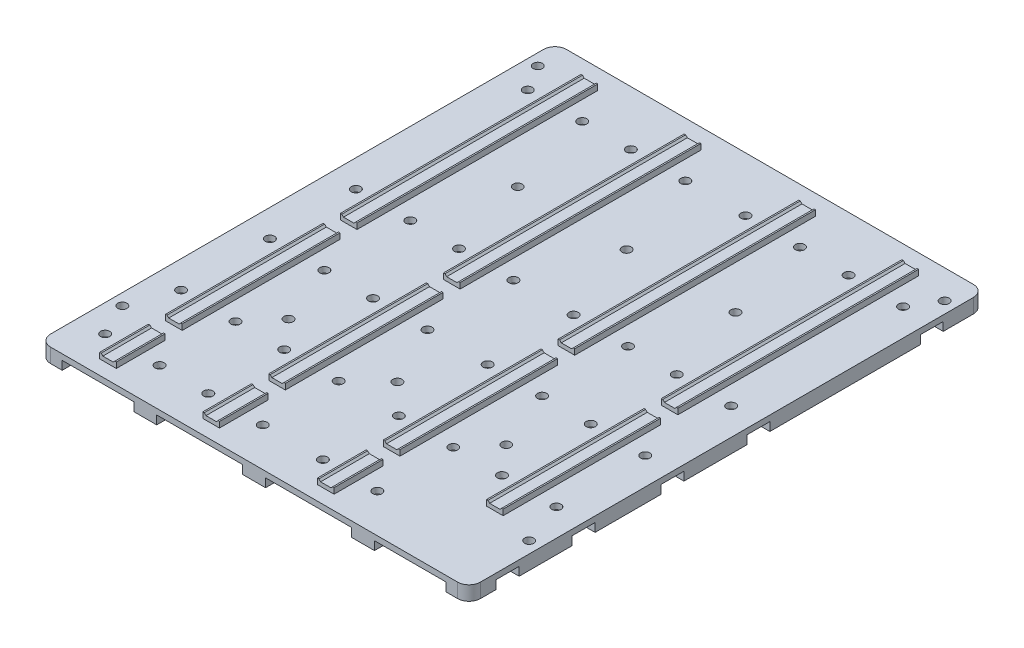
SolidWorks part; units mm, degrees
ref_plane "Front Plane" through (0, 0, 0) normal (0, 0, 1) x (1, 0, 0)
ref_plane "Top Plane" through (0, 0, 0) normal (0, 1, 0) x (1, 0, 0)
ref_plane "Right Plane" through (0, 0, 0) normal (1, 0, 0) x (0, 0, -1)
sketch "Sketch1" plane through (0, 0, 0) normal (0, 1, 0) x (1, 0, 0)
  line L1 (-75, -90) -> (75, -90)
  line L2 (-75, -90) -> (-75, 90)
  line L3 (-75, 90) -> (75, 90)
  line L4 (75, -90) -> (75, 90)
  line L5 (-75, -90) -> (75, 90) construction
  line L6 (-75, 90) -> (75, -90) construction
  point P0 (0, 0)
  dimension "D1" = 150
  dimension "D2" = 180
extrude "Boss-Extrude1" add sketch "Sketch1" along normal blind 2
sketch "Sketch2" plane through (0, 2, 0) normal (0, 1, 0) x (1, 0, 0)
  line L0 (-75, -90) -> (75, -90) construction
  line L1 (-58.9, -7) -> (-53.1, -7)
  line L2 (-58.9, -7) -> (-58.9, -85)
  line L3 (-58.9, -85) -> (-53.1, -85)
  line L4 (-53.1, -7) -> (-53.1, -85)
  line L5 (-22.9, -7) -> (-17.1, -7)
  line L6 (-22.9, -7) -> (-22.9, -85)
  line L7 (-22.9, -85) -> (-17.1, -85)
  line L8 (-17.1, -7) -> (-17.1, -85)
  line L9 (17.1, -7) -> (22.9, -7)
  line L10 (17.1, -7) -> (17.1, -85)
  line L11 (17.1, -85) -> (22.9, -85)
  line L12 (22.9, -7) -> (22.9, -85)
  line L13 (53.1, -7) -> (58.9, -7)
  line L14 (53.1, -7) -> (53.1, -85)
  line L15 (53.1, -85) -> (58.9, -85)
  line L16 (58.9, -7) -> (58.9, -85)
  line L17 (-75, 90) -> (-75, -90) construction
  line L18 (75, -90) -> (75, 90) construction
  line L19 (75, 90) -> (-75, 90) construction
  line L20 (-58.9, -62) -> (58.9, -62)
  line L21 (-58.9, -62) -> (-58.9, -68)
  line L22 (-58.9, -68) -> (58.9, -68)
  line L23 (58.9, -62) -> (58.9, -68)
  line L24 (-58.9, -1) -> (-53.1, -1)
  line L25 (-58.9, -1) -> (-58.9, 83)
  line L26 (-58.9, 83) -> (-53.1, 83)
  line L27 (-53.1, -1) -> (-53.1, 83)
  line L28 (-22.9, -1) -> (-17.1, -1)
  line L29 (-22.9, -1) -> (-22.9, 83)
  line L30 (-22.9, 83) -> (-17.1, 83)
  line L31 (-17.1, -1) -> (-17.1, 83)
  line L32 (17.1, -1) -> (22.9, -1)
  line L33 (17.1, -1) -> (17.1, 83)
  line L34 (17.1, 83) -> (22.9, 83)
  line L35 (22.9, -1) -> (22.9, 83)
  line L36 (53.1, -1) -> (58.9, -1)
  line L37 (53.1, -1) -> (53.1, 83)
  line L38 (53.1, 83) -> (58.9, 83)
  line L39 (58.9, -1) -> (58.9, 83)
  dimension "D1" = 5
  dimension "D2" = 16.1
  dimension "D3" = 5.8
  dimension "D4" = 78
  dimension "D5" = 52.1
  dimension "D6" = 5.8
  dimension "D7" = 5
  dimension "D8" = 5
  dimension "D9" = 5.8
  dimension "D10" = 5.8
  dimension "D11" = 5
  dimension "D12" = 16.1
  dimension "D13" = 52.1
  dimension "D14" = 22
  dimension "D15" = 6
  dimension "D16" = 16.1
  dimension "D17" = 5.8
  dimension "D18" = 6
  dimension "D19" = 7
  dimension "D20" = 7
  dimension "D21" = 7
  dimension "D22" = 7
  dimension "D23" = 52.1
  dimension "D24" = 16.1
  dimension "D25" = 52.1
  dimension "D26" = 5.8
  dimension "D27" = 5.8
  dimension "D28" = 5.8
  dimension "D29" = 6
  dimension "D30" = 6
  dimension "D31" = 6
extrude "Boss-Extrude2" add sketch "Sketch2" along normal blind 2 contours L2 L20 L4 L1 | L22 L2 L3 L4 | L6 L20 L8 L5 | L22 L6 L7 L8 | L10 L20 L12 L9 | L22 L10 L11 L12 | L14 L20 L16 L13 | L25 L24 L27 L26 | L29 L28 L31 L30 | L33 L32 L35 L34 | L37 L36 L39 L38
sketch "Sketch3" plane through (0, 2, 0) normal (0, 1, 0) x (1, 0, 0)
  line L0 (-75, -90) -> (75, -90) construction
  line L1 (-56, -7) -> (-56, -62) construction
  line L2 (-58.9, -7) -> (-53.1, -7) construction
  line L3 (-58.9, -68) -> (-58.9, -85) construction
  line L4 (-53.1, -68) -> (-53.1, -85) construction
  line L5 (17.1, -68) -> (17.1, -85) construction
  line L6 (22.9, -68) -> (22.9, -85) construction
  line L9 (-22.9, -68) -> (-22.9, -85) construction
  line L10 (-17.1, -68) -> (-17.1, -85) construction
  line L11 (-58.9, -62) -> (-53.1, -62) construction
  line L12 (-56, -1) -> (-56, 83) construction
  line L13 (-58.9, -1) -> (-53.1, -1) construction
  line L16 (-22.9, -7) -> (-22.9, -62) construction
  line L17 (-17.1, -7) -> (-17.1, -62) construction
  line L18 (17.1, -7) -> (17.1, -62) construction
  line L19 (22.9, -7) -> (22.9, -62) construction
  line L20 (53.1, -7) -> (53.1, -62) construction
  line L21 (58.9, -7) -> (58.9, -62) construction
  line L22 (-58.9, 83) -> (-53.1, 83) construction
  line L25 (-22.9, -1) -> (-22.9, 83) construction
  line L26 (-17.1, -1) -> (-17.1, 83) construction
  line L27 (17.1, -1) -> (17.1, 83) construction
  line L28 (22.9, -1) -> (22.9, 83) construction
  line L29 (53.1, -1) -> (53.1, 83) construction
  line L30 (58.9, -1) -> (58.9, 83) construction
  line L33 (-58.9, 83) -> (-53.1, 83) construction
  line L34 (-58.9, -7) -> (-53.1, -7) construction
  line L35 (-58.9, -7) -> (-58.9, -62) construction
  line L36 (-53.1, -7) -> (-53.1, -62) construction
  line L37 (-17.1, -7) -> (-17.1, -62) construction
  line L38 (17.1, -7) -> (17.1, -62) construction
  line L39 (22.9, -7) -> (22.9, -62) construction
  line L40 (58.9, -7) -> (58.9, -62) construction
  line L41 (-58.9, -1) -> (-58.9, 83) construction
  line L42 (-53.1, -1) -> (-53.1, 83) construction
  line L43 (22.9, -1) -> (22.9, 83) construction
  line L44 (53.1, -1) -> (53.1, 83) construction
  circle A0 centre (-65.5, -76.5) radius 1.6
  circle A1 centre (-46.5, -76.5) radius 1.6
  circle A2 centre (-29.5, -76.5) radius 1.6
  circle A3 centre (-10.5, -76.5) radius 1.6
  circle A4 centre (10.5, -76.5) radius 1.6
  circle A5 centre (29.5, -76.5) radius 1.6
  circle A10 centre (-65.5, -50) radius 1.6
  circle A11 centre (-46.5, -50) radius 1.6
  circle A12 centre (-29.5, -50) radius 1.6
  circle A13 centre (-10.5, -50) radius 1.6
  circle A17 centre (10.5, -50) radius 1.6
  circle A18 centre (29.5, -50) radius 1.6
  circle A22 centre (46.5, -50) radius 1.6
  circle A23 centre (65.5, -50) radius 1.6
  circle A24 centre (65.5, 11) radius 1.6
  circle A25 centre (-65.5, 11) radius 1.6
  circle A26 centre (10.5, 11) radius 1.6
  circle A27 centre (-29.5, 11) radius 1.6
  circle A28 centre (-46.5, 11) radius 1.6
  circle A29 centre (46.5, 11) radius 1.6
  circle A30 centre (29.5, 11) radius 1.6
  circle A31 centre (-10.5, 11) radius 1.6
  circle A32 centre (10.5, 71) radius 1.6
  circle A33 centre (65.5, 71) radius 1.6
  circle A34 centre (29.5, 71) radius 1.6
  circle A35 centre (-46.5, 71) radius 1.6
  circle A36 centre (-65.5, 71) radius 1.6
  circle A37 centre (-29.5, 71) radius 1.6
  circle A38 centre (-10.5, 71) radius 1.6
  circle A39 centre (46.5, 71) radius 1.6
  circle A40 centre (-65.5, -19) radius 1.6
  circle A41 centre (10.5, -19) radius 1.6
  circle A42 centre (65.5, -19) radius 1.6
  circle A43 centre (-46.5, -19) radius 1.6
  circle A44 centre (-29.5, -19) radius 1.6
  circle A45 centre (29.5, -19) radius 1.6
  circle A46 centre (46.5, -19) radius 1.6
  circle A47 centre (-10.5, -19) radius 1.6
  dimension "D1" = 3.2
  dimension "D12" = 3.2
  dimension "D21" = 9.5
  dimension "D22" = 9.5
  dimension "D27" = 6.6
  dimension "D30" = 12
  dimension "D2" = 13.5
  dimension "D3" = 6.6
  dimension "D4" = 6.6
  dimension "D5" = 6.6
  dimension "D6" = 6.6
  dimension "D7" = 6.6
  dimension "D8" = 6.6
  dimension "D9" = 6.6
  dimension "D10" = 6.6
  dimension "D11" = 40
  dimension "D13" = 9.5
  dimension "D14" = 9.5
  dimension "D15" = 6.6
  dimension "D16" = 6.6
  dimension "D17" = 6.6
  dimension "D18" = 6.6
  dimension "D19" = 6.6
  dimension "D20" = 6.6
  dimension "D23" = 6.6
  dimension "D24" = 6.6
  dimension "D25" = 6.6
  dimension "D26" = 6.6
  dimension "D28" = 6.6
  dimension "D29" = 12
  dimension "D31" = 12
  dimension "D32" = 6.6
  dimension "D33" = 6.6
  dimension "D34" = 6.6
  dimension "D35" = 6.6
  dimension "D36" = 6.6
  dimension "D37" = 6.6
  dimension "D38" = 6.6
  dimension "D39" = 6.6
  dimension "D40" = 6.6
  dimension "D41" = 6.6
  dimension "D42" = 6.6
  dimension "D43" = 6.6
  dimension "D44" = 6.6
  dimension "D45" = 6.6
extrude "Cut-Extrude1" cut sketch "Sketch3" against normal through all
sketch "Sketch4" plane through (0, 0, 85) normal (0, 0, 1) x (1, 0, 0)
  line L0 (-58.9, 4) -> (-58.4, 4)
  line L1 (-58.9, 4) -> (-53.1, 4) construction
  line L2 (-58.4, 4) -> (-57.8, 3.4)
  line L3 (-57.8, 3.4) -> (-54.2, 3.4)
  line L4 (-54.2, 3.4) -> (-53.6, 4)
  line L5 (-53.6, 4) -> (-58.4, 4)
  line L6 (-22.4, 4) -> (-21.8, 3.4)
  line L7 (-22.9, 4) -> (-17.1, 4) construction
  line L8 (-21.8, 3.4) -> (-18.2, 3.4)
  line L9 (-18.2, 3.4) -> (-17.6, 4)
  line L10 (-17.6, 4) -> (-22.4, 4)
  line L11 (0, 0) -> (0, 11.932) construction
  line L12 (17.6, 4) -> (22.4, 4)
  line L13 (18.2, 3.4) -> (17.6, 4)
  line L14 (21.8, 3.4) -> (18.2, 3.4)
  line L15 (22.4, 4) -> (21.8, 3.4)
  line L16 (53.6, 4) -> (58.4, 4)
  line L17 (54.2, 3.4) -> (53.6, 4)
  line L18 (57.8, 3.4) -> (54.2, 3.4)
  line L19 (58.4, 4) -> (57.8, 3.4)
  line L20 (58.9, 4) -> (58.4, 4)
  line M13 (-53.1, 4) -> (-58.9, 4)
  dimension "D1" = 0.5
  dimension "D2" = 0.5
  dimension "D3" = 45
  dimension "D4" = 45
  dimension "D5" = 0.6
  dimension "D6" = 0.5
  dimension "D7" = 0.5
  dimension "D8" = 45
  dimension "D9" = 0.6
extrude "Cut-Extrude2" cut sketch "Sketch4" against normal through all contours L3 L4 L2 M13 | L9 L10 L6 L8 | L15 L12 L13 L14 | L19 L16 L17 L18
sketch "Sketch5" plane through (0, 0, 90) normal (0, 0, 1) x (1, 0, 0)
  line L0 (-75, 0) -> (75, 0) construction
  line L1 (-75, 0) -> (-67, 0)
  line L2 (-75, 0) -> (-75, -3)
  line L3 (-75, -3) -> (-67, -3)
  line L4 (-67, 0) -> (-67, -3)
  line L5 (75, 0) -> (67, 0)
  line L6 (75, 0) -> (75, -3)
  line L7 (75, -3) -> (67, -3)
  line L8 (67, 0) -> (67, -3)
  line L9 (-42, 0) -> (-34, 0)
  line L10 (-42, 0) -> (-42, -3)
  line L11 (-42, -3) -> (-34, -3)
  line L12 (-34, 0) -> (-34, -3)
  line L13 (75, 2) -> (75, 0) construction
  line L14 (-4, 0) -> (4, 0)
  line L15 (-4, 0) -> (-4, -3)
  line L16 (-4, -3) -> (4, -3)
  line L17 (4, 0) -> (4, -3)
  line L18 (34, 0) -> (42, 0)
  line L19 (34, 0) -> (34, -3)
  line L20 (34, -3) -> (42, -3)
  line L21 (42, 0) -> (42, -3)
  line L22 (-75, 2) -> (-75, 0) construction
  line L23 (-22.9, 2) -> (-53.1, 2) construction
  dimension "D1" = 8
  dimension "D2" = 3
  dimension "D3" = 8
  dimension "D4" = 3
  dimension "D5" = 8
  dimension "D6" = 3
  dimension "D7" = 4
  dimension "D8" = 8
  dimension "D9" = 3
  dimension "D10" = 8
  dimension "D11" = 3
  dimension "D12" = 33
  dimension "D13" = 33
extrude "Boss-Extrude3" add sketch "Sketch5" against normal through all contours L2 L1 L4 L3 | L10 L9 L12 L11 | L15 L14 L17 L16 | L19 L18 L21 L20 | L6 L5 L8 L7
sketch "Sketch6" plane through (0, 2, 0) normal (0, 1, 0) x (1, 0, 0)
  line L0 (75, 90) -> (-75, 90) construction
  line L1 (-75, 90) -> (-75, -90) construction
  line L2 (75, -90) -> (75, 90) construction
  line L3 (-75, -90) -> (75, -90) construction
  circle A0 centre (-38, -40) radius 1.6
  circle A1 centre (38, -40) radius 1.6
  circle A2 centre (0, -40) radius 1.6
  circle A3 centre (-38, 40) radius 1.6
  circle A4 centre (0, 40) radius 1.6
  circle A5 centre (38, 40) radius 1.6
  circle A6 centre (-71, -65) radius 1.6
  circle A7 centre (71, -65) radius 1.6
  circle A8 centre (71, 80) radius 1.6
  circle A9 centre (-71, 80) radius 1.6
  dimension "D1" = 3.2
  dimension "D2" = 50
  dimension "D6" = 50
  dimension "D10" = 3.2
  dimension "D13" = 3.2
  dimension "D16" = 3.2
  dimension "D19" = 3.2
  dimension "D3" = 37
  dimension "D4" = 37
  dimension "D5" = 75
  dimension "D7" = 37
  dimension "D8" = 75
  dimension "D9" = 37
  dimension "D11" = 4
  dimension "D12" = 10
  dimension "D14" = 25
  dimension "D15" = 4
  dimension "D17" = 4
  dimension "D18" = 25
  dimension "D20" = 4
  dimension "D21" = 10
extrude "Cut-Extrude3" cut sketch "Sketch6" against normal blind 10
sketch "Sketch7" plane through (0, -3, 0) normal (0, -1, 0) x (1, 0, 0)
  line L0 (-75, -90) -> (-75, 90) construction
  line L1 (-75, 80.5) -> (-57.3327, 80.5)
  line L2 (-75, 80.5) -> (-75, 72.5)
  line L3 (-75, 72.5) -> (-57.3327, 72.5)
  line L4 (75, 80.5) -> (75, 72.5)
  line L5 (75, -90) -> (75, 90) construction
  line L6 (-67, 90) -> (-42, 90) construction
  line L7 (-75, 54) -> (-57.3327, 54)
  line L8 (-75, 54) -> (-75, 46)
  line L9 (-75, 46) -> (-57.3327, 46)
  line L10 (75, 54) -> (75, 46)
  line L11 (-75, 23) -> (-57.3327, 23)
  line L12 (-75, 23) -> (-75, 15)
  line L13 (-75, 15) -> (-57.3327, 15)
  line L14 (75, 23) -> (75, 15)
  line L15 (-75, -7) -> (-57.3327, -7)
  line L16 (-75, -7) -> (-75, -15)
  line L17 (-75, -15) -> (-57.3327, -15)
  line L18 (75, -7) -> (75, -15)
  line L19 (-75, -67.5) -> (-57.3327, -67.5)
  line L20 (-75, -67.5) -> (-75, -75.5)
  line L21 (-75, -75.5) -> (-57.3327, -75.5)
  line L22 (75, -67.5) -> (75, -75.5)
  line L23 (-42, -90) -> (-67, -90) construction
  line L24 (-57.3327, 80.5) -> (-57.3327, 72.5)
  line L25 (52.1549, 80.5) -> (52.1549, 72.5)
  line L26 (52.1549, 80.5) -> (75, 80.5)
  line L27 (52.1549, 72.5) -> (75, 72.5)
  line L28 (52.1549, 54) -> (75, 54)
  line L29 (52.1549, 46) -> (75, 46)
  line L30 (52.1549, 23) -> (75, 23)
  line L31 (52.1549, 15) -> (75, 15)
  line L32 (52.1549, -7) -> (75, -7)
  line L33 (52.1549, -15) -> (75, -15)
  line L34 (52.1549, -67.5) -> (75, -67.5)
  line L35 (52.1549, -75.5) -> (75, -75.5)
  line L36 (-57.3327, 54) -> (-57.3327, 46)
  line L37 (-57.3327, 23) -> (-57.3327, 15)
  line L38 (-57.3327, -7) -> (-57.3327, -15)
  line L39 (-57.3327, -67.5) -> (-57.3327, -75.5)
  line L40 (52.1549, -67.5) -> (52.1549, -75.5)
  line L41 (52.1549, -7) -> (52.1549, -15)
  line L42 (52.1549, 23) -> (52.1549, 15)
  line L43 (52.1549, 54) -> (52.1549, 46)
  dimension "D2" = 8
  dimension "D3" = 36
  dimension "D5" = 67
  dimension "D7" = 14.5
  dimension "D9" = 75
  dimension "D1" = 9.5
  dimension "D4" = 8
  dimension "D6" = 8
  dimension "D8" = 8
  dimension "D10" = 8
extrude "Cut-Extrude4" cut sketch "Sketch7" against normal blind 3
fillet "Fillet1" radius 4 4 edges at (75, -0.5, 90) (-75, -0.5, 90) (-75, -0.5, -90) (75, -0.5, -90)
